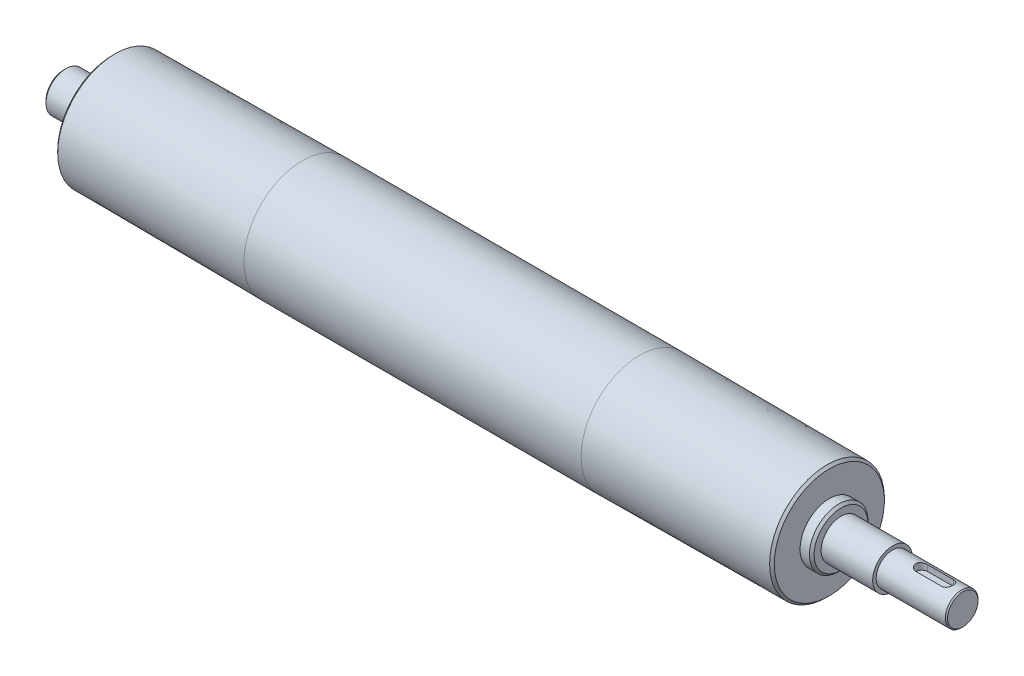
SolidWorks part; units mm, degrees
material "Alloy Steel"
ref_plane "Front Plane" through (0, 0, 0) normal (0, 0, 1) x (1, 0, 0)
ref_plane "Top Plane" through (0, 0, 0) normal (0, 1, 0) x (1, 0, 0)
ref_plane "Right Plane" through (0, 0, 0) normal (1, 0, 0) x (0, 0, -1)
sketch "Sketch1" plane through (0, 0, 0) normal (0, 1, 0) x (1, 0, 0)
  line L0 (-72, 25) -> (72, 25)
  line L1 (0, 0) -> (0, 25) construction
  line L2 (-72, 25) -> (-152, 24.5)
  line L3 (72, 25) -> (152, 24.5)
  line L4 (-174, 0) -> (210, 0)
  line L5 (-152, 24.5) -> (-153, 23.5)
  line L6 (152, 24.5) -> (153, 23.5)
  line L7 (153, 23.5) -> (153, 12.5)
  line L8 (153, 12.5) -> (157, 12.5)
  line L9 (157, 12.5) -> (158, 11.5)
  line L10 (158, 11.5) -> (158, 8.5)
  line L11 (158, 8.5) -> (180, 8.5)
  line L12 (209.5, 7) -> (210, 6.5)
  line L13 (180, 8.5) -> (180, 7)
  line L14 (-153, 23.5) -> (-153, 12.5)
  line L15 (-153, 12.5) -> (-157, 12.5)
  line L16 (-157, 12.5) -> (-158, 11.5)
  line L17 (-158, 11.5) -> (-158, 8.5)
  line L18 (-158, 8.5) -> (-173, 8.5)
  line L19 (-173, 8.5) -> (-174, 7.5)
  line L20 (-174, 7.5) -> (-174, 0)
  line L21 (180, 7) -> (209.5, 7)
  line L22 (210, 6.5) -> (210, 0)
  dimension "D1" = 25
  dimension "D2" = 80
  dimension "D3" = 80
  dimension "D4" = 24.5
  dimension "D5" = 24.5
  dimension "D6" = 45
  dimension "D7" = 1
  dimension "D8" = 45
  dimension "D9" = 1
  dimension "D10" = 12.5
  dimension "D11" = 5
  dimension "D12" = 135
  dimension "D13" = 1
  dimension "D14" = 8.5
  dimension "D15" = 0.5
  dimension "D16" = 22
  dimension "D17" = 135
  dimension "D18" = 1
  dimension "D19" = 1
  dimension "D20" = 12.5
  dimension "D21" = 8.5
  dimension "D22" = 5
  dimension "D23" = 16
  dimension "D24" = 306
  dimension "D25" = 135
  dimension "D26" = 7
  dimension "D27" = 30
revolve "Revolve1" add sketch "Sketch1" angle 360 about L4
ref_plane "Plane1" through (0, 4, 0) normal (0, 1, 0) x (-1, 0, 0)
sketch "Sketch2" plane through (0, 4, 0) normal (0, 1, 0) x (-1, 0, 0)
  line L0 (-210, 6.5) -> (-210, -6.5) construction
  line L1 (-210, 6.5) -> (-210, -6.5)
  line L2 (-206, 0) -> (-190, 0) construction
  line L3 (-203.5, 2.5) -> (-192.5, 2.5)
  line L4 (-203.5, -2.5) -> (-192.5, -2.5)
  line L5 (-158, 8.5) -> (-158, -8.5) construction
  line L6 (-158, 8.5) -> (-158, -8.5)
  arc A0 (-203.5, 2.5) -> (-203.5, -2.5) centre (-203.5, 0) ccw
  arc A1 (-192.5, -2.5) -> (-192.5, 2.5) centre (-192.5, 0) ccw
  dimension "D1" = 2.5
  dimension "D2" = 2.5
  dimension "D3" = 32
  dimension "D4" = 16
extrude "Extrude1" cut sketch "Sketch2" along normal through all contours L4 A1 L3 A0
